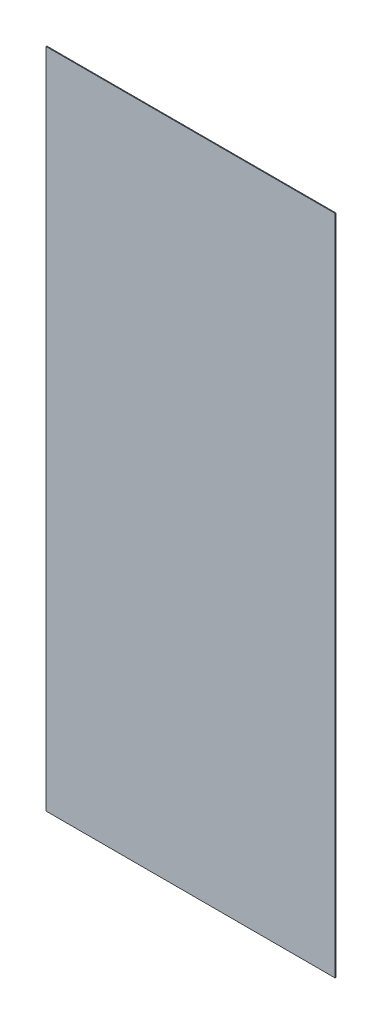
SolidWorks part; units mm, degrees
material "3.0205 (EN-AW 1200)"
ref_plane "정면" through (0, 0, 0) normal (0, 0, 1) x (1, 0, 0)
ref_plane "윗면" through (0, 0, 0) normal (0, 1, 0) x (1, 0, 0)
ref_plane "우측면" through (0, 0, 0) normal (1, 0, 0) x (0, 0, -1)
sketch "스케치1" plane through (0, 0, 0) normal (0, 0, 1) x (1, 0, 0)
  line L1 (0, 0) -> (358, 0)
  line L2 (0, 0) -> (0, 820)
  line L3 (0, 820) -> (358, 820)
  line L4 (358, 0) -> (358, 820)
  dimension "D1" = 820
  dimension "D2" = 358
extrude "보스-돌출1" add sketch "스케치1" along normal blind 1
